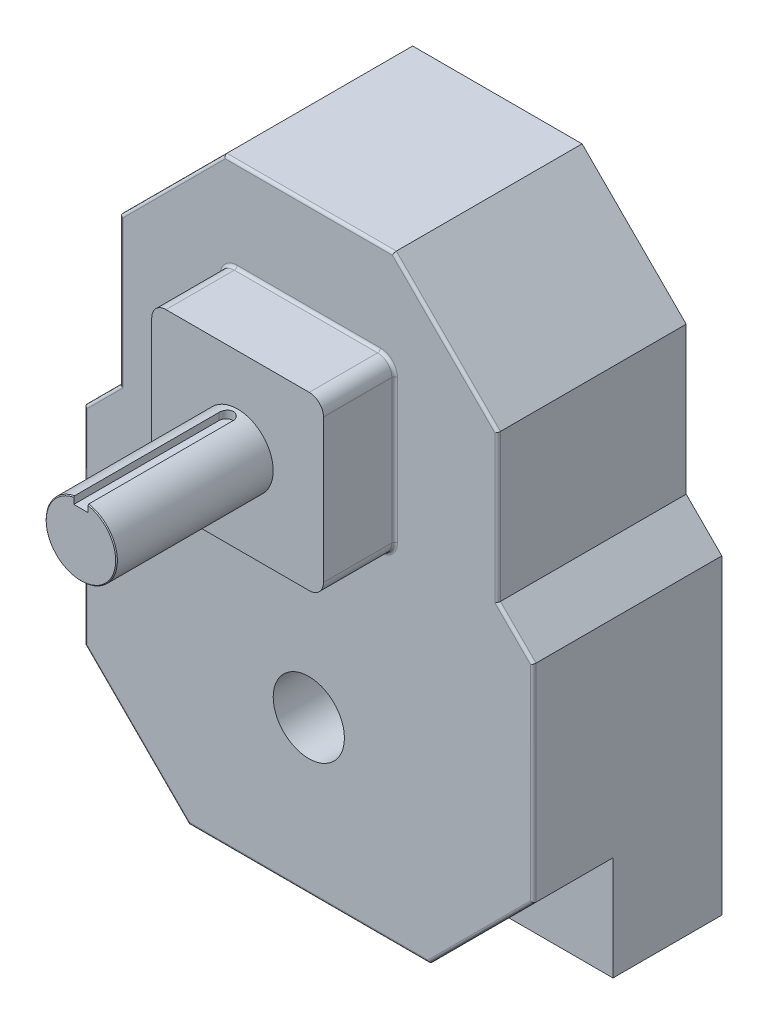
SolidWorks part; units mm, degrees
ref_plane "Front Plane" through (0, 0, 0) normal (0, 0, 1) x (1, 0, 0)
ref_plane "Top Plane" through (0, 0, 0) normal (0, 1, 0) x (1, 0, 0)
ref_plane "Right Plane" through (0, 0, 0) normal (1, 0, 0) x (0, 0, -1)
ref_plane "G" through (0, 136.652, 0) normal (0, 1, 0) x (-1, 0, 0)
ref_plane "E" through (0, 255.778, 0) normal (0, 1, 0) x (-1, 0, 0)
ref_plane "J" through (0, 335.026, 0) normal (0, 1, 0) x (-1, 0, 0)
ref_plane "B" through (0, 0, 84.074) normal (0, 0, 1) x (1, 0, 0)
ref_plane "C" through (0, 0, 185.674) normal (0, 0, 1) x (1, 0, 0)
ref_plane "A" through (0, 0, 115.824) normal (0, 0, 1) x (1, 0, 0)
sketch "L,M" plane through (0, 0, 0) normal (0, 0, 1) x (1, 0, 0)
  line L0 (103.4298, 335.026) -> (-37.7786, 335.026) construction
  line L1 (0, 0) -> (0, 136.652) construction
  line L2 (48.895, 136.652) -> (-48.895, 136.652) construction
  line L3 (-100.076, 68.326) -> (100.076, 68.326)
  line L4 (-37.7786, 335.026) -> (37.7786, 335.026)
  line L5 (48.895, 335.026) -> (-48.895, 335.026) construction
  line L6 (37.7786, 335.026) -> (84.201, 288.6036)
  line L7 (84.201, 288.6036) -> (84.201, 222.9524)
  line L8 (84.201, 222.9524) -> (100.076, 207.0774)
  line L9 (100.076, 207.0774) -> (100.076, 68.326)
  line L11 (103.4298, 335.026) -> (37.7786, 335.026) construction
  line L12 (-100.076, 207.0774) -> (-100.076, 68.326)
  line L13 (-84.201, 222.9524) -> (-100.076, 207.0774)
  line L14 (-84.201, 288.6036) -> (-84.201, 222.9524)
  line L15 (-37.7786, 335.026) -> (-84.201, 288.6036)
  line L16 (48.895, 255.778) -> (-48.895, 255.778) construction
  point P0 (-84.201, 255.778)
  point P7 (0, 68.326)
  point P23 (0, 335.026)
  dimension "D1" = 168.402
  dimension "D2" = 200.152
  dimension "D3" = 45
extrude "Boss-Extrude1" add sketch "L,M" along normal up to surface (84.074 mm away) up to plane "B"
sketch "Sketch3" plane through (0, 0, 84.074) normal (0, 0, 1) x (1, 0, 0)
  line L1 (48.895, 255.778) -> (-48.895, 255.778) construction
  line L2 (-38.2905, 294.0685) -> (38.2905, 294.0685)
  line L3 (-38.2905, 294.0685) -> (-38.2905, 217.4875)
  line L4 (-38.2905, 217.4875) -> (38.2905, 217.4875)
  line L5 (38.2905, 294.0685) -> (38.2905, 217.4875)
  line L6 (0, 255.778) -> (0, 0) construction
  line L7 (-38.2905, 294.0685) -> (38.2905, 217.4875) construction
  point P4 (0, 255.778)
  dimension "D1" = 76.581
extrude "Boss-Extrude2" add sketch "Sketch3" along normal up to surface (31.75 mm away) up to plane "A"
sketch "D" plane through (0, 0, 115.824) normal (0, 0, 1) x (1, 0, 0)
  line L0 (-38.2905, 294.0685) -> (38.2905, 217.4875) construction
  circle A0 centre (0, 255.778) radius 15.875
  dimension "D1" = 31.75
extrude "Boss-Extrude3" add sketch "D" along normal up to surface (69.85 mm away) up to plane "C"
sketch "Sketch5" plane through (0, 0, 84.074) normal (0, 0, 1) x (1, 0, 0)
  line L0 (100.076, 114.7484) -> (53.6536, 68.326)
  line L1 (100.076, 68.326) -> (100.076, 207.0774) construction
  line L2 (-100.076, 68.326) -> (100.076, 68.326) construction
  line L3 (53.6536, 68.326) -> (100.076, 68.326)
  line L4 (100.076, 68.326) -> (100.076, 114.7484)
  line L5 (-37.7786, 335.026) -> (-84.201, 288.6036) construction
  line L6 (0, 68.326) -> (0, 255.778) construction
  line L7 (-100.076, 68.326) -> (-100.076, 114.7484)
  line L8 (-53.6536, 68.326) -> (-100.076, 68.326)
  line L9 (-100.076, 114.7484) -> (-53.6536, 68.326)
extrude "Cut-Extrude1" cut sketch "Sketch5" against normal blind 35.56
fillet "Fillet1" radius 6.35 4 edges at (-38.2905, 217.4875, 99.949) (38.2905, 217.4875, 99.949) (-38.2905, 294.0685, 99.949) (38.2905, 294.0685, 99.949)
fillet "Fillet2" radius 1.27 20 edges at (36.4306, 219.3474, 84.074) (38.2905, 255.778, 84.074) (36.4306, 292.2086, 84.074) (0, 294.0685, 84.074) (-36.4306, 292.2086, 84.074) (-38.2905, 255.778, 84.074) (-36.4306, 219.3474, 84.074) (0, 217.4875, 84.074) (-100.076, 160.9129, 84.074) (-92.1385, 215.0149, 84.074) (-84.201, 255.778, 84.074) (-60.9898, 311.8148, 84.074) (0, 335.026, 84.074) (60.9898, 311.8148, 84.074) (84.201, 255.778, 84.074) (92.1385, 215.0149, 84.074) (100.076, 160.9129, 84.074) (76.8648, 91.5372, 84.074) (0, 68.326, 84.074) (-76.8648, 91.5372, 84.074)
sketch "Sketch6" plane through (0, 255.778, 0) normal (0, 1, 0) x (-1, 0, 0)
  line L0 (0, 185.674) -> (0, 120.904) construction
  line L1 (48.895, 185.674) -> (-48.895, 185.674) construction
  line L2 (3.175, 185.674) -> (3.175, 120.904)
  line L3 (-3.175, 185.674) -> (-3.175, 120.904)
  line L4 (0, 0) -> (0, 120.904) construction
  line L6 (-37.7786, 0) -> (37.7786, 0) construction
  line L7 (48.895, 115.824) -> (-48.895, 115.824) construction
  arc A0 (3.175, 185.674) -> (-3.175, 185.674) centre (0, 185.674) ccw
  arc A1 (-3.175, 120.904) -> (3.175, 120.904) centre (0, 120.904) ccw
  point P4 (0, 153.289)
  dimension "D2" = 5.08
  dimension "D1" = 6.35
extrude "Keyway" cut sketch "Sketch6" along normal through all from offset 12.3698
chamfer "Chamfer1" distance 0.381 angle 45 1 edges at (0, 239.903, 185.674)
sketch "Sketch7" plane through (0, 0, 0) normal (0, 0, -1) x (-1, 0, 0)
  line L0 (48.895, 136.652) -> (-48.895, 136.652) construction
  line L1 (0, 136.652) -> (0, 255.778) construction
  circle A0 centre (0, 136.652) radius 15.875
  circle A1 centre (0, 255.778) radius 15.875 construction
extrude "Cut-Extrude3" cut sketch "Sketch7" against normal through all
